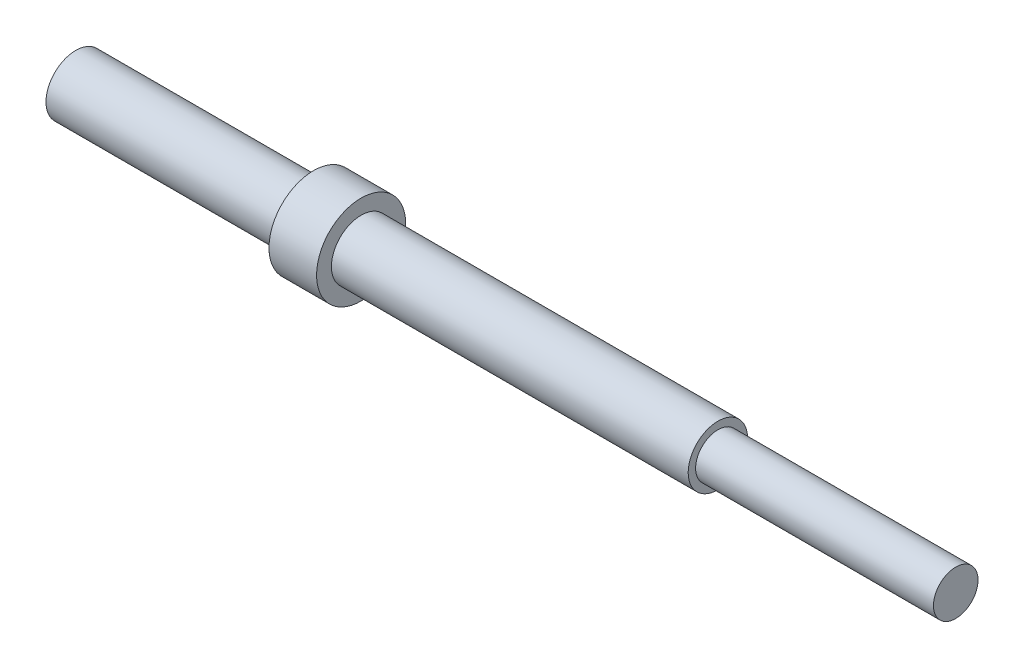
SolidWorks part; units mm, degrees
ref_plane "Front Plane" through (0, 0, 0) normal (0, 0, 1) x (1, 0, 0)
ref_plane "Top Plane" through (0, 0, 0) normal (0, 1, 0) x (1, 0, 0)
ref_plane "Right Plane" through (0, 0, 0) normal (1, 0, 0) x (0, 0, -1)
sketch "Sketch1" plane through (0, 0, 0) normal (0, 0, 1) x (1, 0, 0)
  line L0 (0, 0) -> (13999.5626, 0) construction
  line L1 (0, 1.905) -> (38.1, 1.905)
  line L2 (38.1, 1.905) -> (38.1, 0)
  line L3 (0, 1.905) -> (0, 3.175)
  line L4 (0, 3.175) -> (25.4, 3.175)
  line L5 (25.4, 3.175) -> (25.4, 4.7625)
  line L6 (25.4, 4.7625) -> (30.48, 4.7625)
  line L7 (30.48, 4.7625) -> (30.48, 3.175)
  line L8 (30.48, 3.175) -> (68.58, 3.175)
  line L9 (68.58, 3.175) -> (68.58, 2.3813)
  line L10 (68.58, 2.3813) -> (93.98, 2.3813)
  line L11 (93.98, 2.3813) -> (93.98, 0)
  line L12 (38.1, 0) -> (93.98, 0)
  line L13 (93.98, 0) -> (94.0441, 0.0261)
  point P14 (38.1, 0.9525)
  point P16 (0, 2.54)
  dimension "D1" = 3.81
  dimension "D2" = 38.1
  dimension "D3" = 25.4
  dimension "D4" = 5.08
  dimension "D5" = 38.1
  dimension "D6" = 25.4
  dimension "D7" = 4.7625
  dimension "D8" = 6.35
  dimension "D9" = 9.525
  dimension "D10" = 6.35
revolve "Revolve1" add sketch "Sketch1" angle 360 about L0
